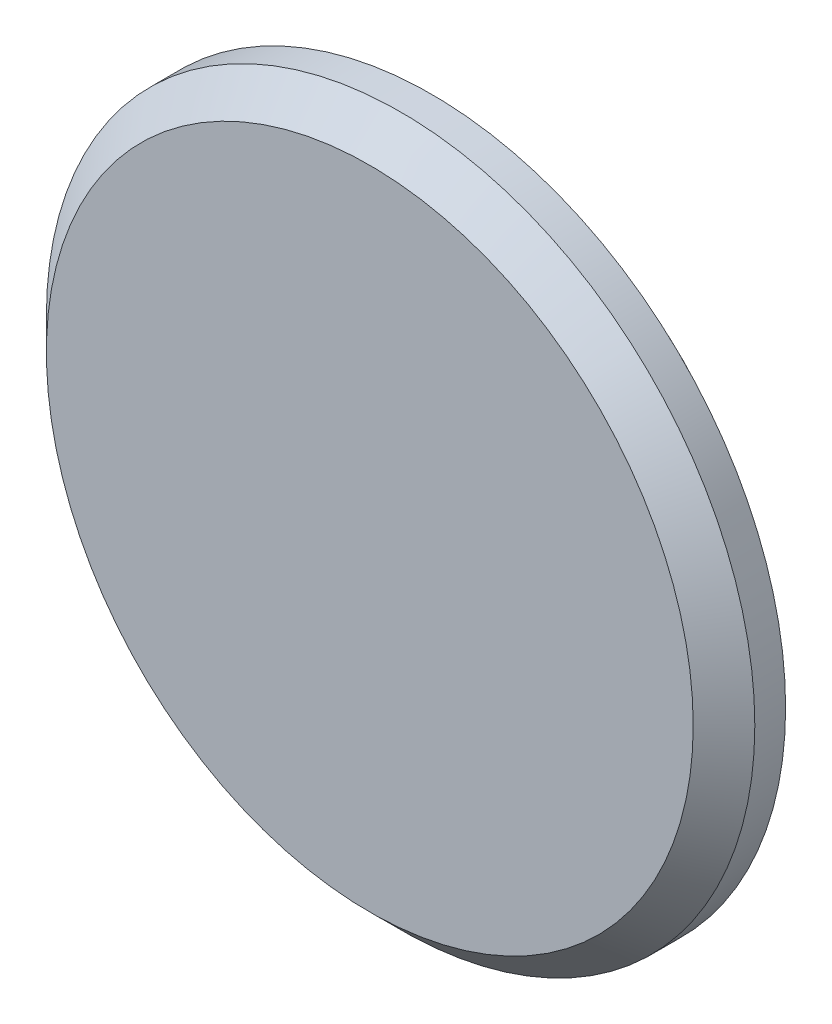
SolidWorks part; units mm, degrees
material "PET"
ref_plane "Front Plane" through (0, 0, 0) normal (0, 0, 1) x (1, 0, 0)
ref_plane "Top Plane" through (0, 0, 0) normal (0, 1, 0) x (1, 0, 0)
ref_plane "Right Plane" through (0, 0, 0) normal (1, 0, 0) x (0, 0, -1)
sketch "Sketch1" plane through (0, 0, 0) normal (0, 0, 1) x (1, 0, 0)
  circle A2 centre (0, 0) radius 30.0863
  circle A3 centre (0, 0) radius 30.0863
  dimension "D1" = 1.27
extrude "Boss-Extrude1" add sketch "Sketch1" against normal blind 6.35
sketch "Sketch2" plane through (0, 0, 0) normal (0, 0, 1) x (1, 0, 0)
  circle A0 centre (0, 0) radius 36.5125
extrude "Boss-Extrude2" add sketch "Sketch2" along normal blind 6.35
chamfer "Chamfer1" distance 3.175 angle 45 1 edges at (36.5125, 0, 6.35)
chamfer "Chamfer2" distance 2.54 angle 45 1 edges at (30.0863, 0, -6.35)
